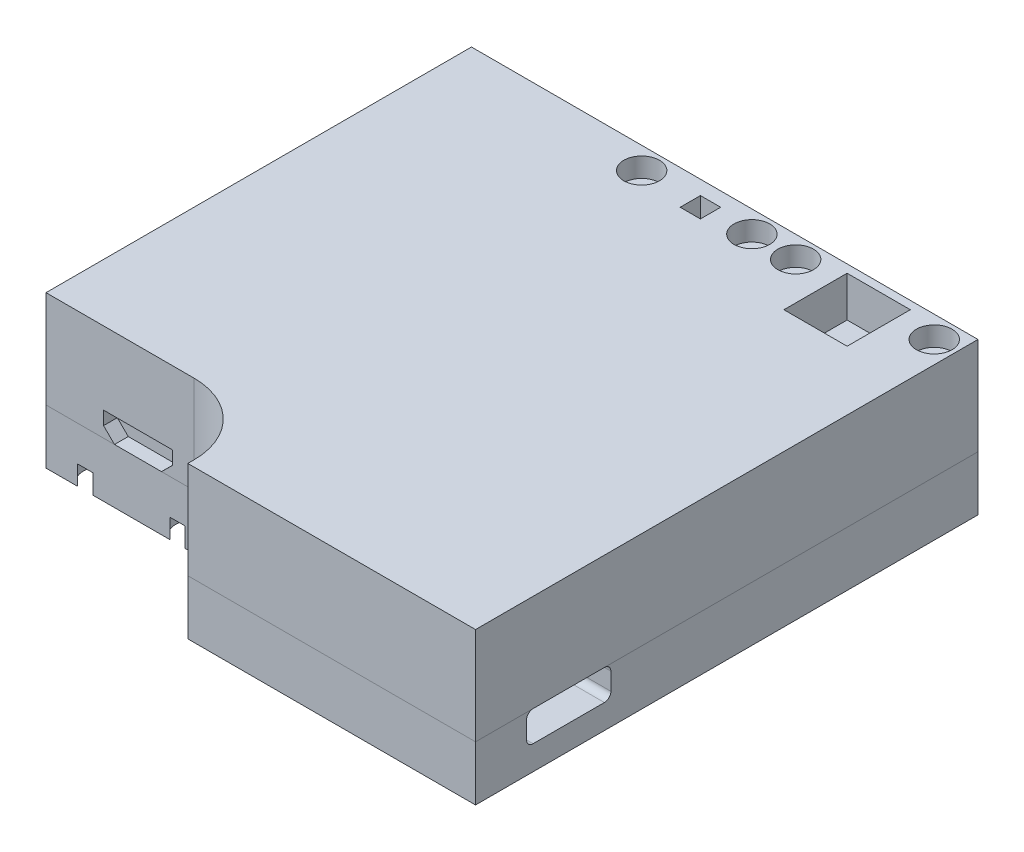
SolidWorks part; units mm, degrees
ref_plane "Front Plane" through (0, 0, 0) normal (0, 0, 1) x (1, 0, 0)
ref_plane "Top Plane" through (0, 0, 0) normal (0, 1, 0) x (1, 0, 0)
ref_plane "Right Plane" through (0, 0, 0) normal (1, 0, 0) x (0, 0, -1)
sketch "Sketch2" plane through (0, 0, 0) normal (0, 1, 0) x (1, 0, 0)
  line L0 (0, 62) -> (0, 0)
  line L1 (-62.5, 62) -> (0, 62)
  line L2 (-62.5, 62) -> (-62.5, 9.5)
  line L4 (0, 62) -> (0, 0)
  line L5 (0, 0) -> (-35.5, 0)
  line L6 (-35.5, 0) -> (-35.5, 9.5)
  line L7 (-35.5, 9.5) -> (-62.5, 9.5)
  dimension "D1" = 52.5
  dimension "D2" = 62.5
  dimension "D3" = 62
  dimension "D4" = 35.5
  dimension "D5" = 9.5
  dimension "D6" = 27
extrude "Boss-Extrude1" add sketch "Sketch2" along normal blind 12 and the other way blind 6.75 contours L7 L6 L5 L0 L1 L2
sketch "Sketch5" plane through (0, 12, 0) normal (0, 1, 0) x (1, 0, 0)
  line L0 (-57.7, 62) -> (-57.7, 60)
  line L1 (-62.5, 62) -> (0, 62) construction
  line L2 (-57.7, 60) -> (-62.5, 60)
  line L3 (-62.5, 62) -> (-62.5, 9.5) construction
  line L4 (-57.7, 60) -> (-46.3, 60)
  line L5 (-46.3, 60) -> (-46.3, 62)
  line L6 (-46.3, 60) -> (-41.5, 60)
  line L7 (-41.5, 60) -> (-41.5, 61.5)
  line L8 (-38.8, 62) -> (-38.8, 59.3)
  line L9 (-38.8, 59.3) -> (-41.5, 59.3)
  line L10 (-41.5, 59.3) -> (-41.5, 60)
  line L11 (-38.8, 59.3) -> (-25.2, 59.3)
  line L12 (-25.2, 59.3) -> (-25.2, 62)
  line L13 (-25.2, 59.3) -> (-22.5, 59.3)
  line L14 (-22.5, 59.3) -> (-22.5, 62)
  line L15 (-22.5, 59.3) -> (-19.8, 59.3)
  line L16 (-19.8, 59.3) -> (-19.8, 62)
  line L17 (-62.5, 62) -> (0, 62) construction
  line L18 (-19.8, 59.3) -> (-2.7, 59.3)
  line L19 (-2.7, 59.3) -> (-2.7, 61.5)
  line L20 (-2.7, 59.3) -> (0, 59.3)
  line L21 (0, 62) -> (0, 0) construction
  line L22 (-57.7, 60) -> (-57.7, 9.5)
  line L23 (-35.5, 9.5) -> (-62.5, 9.5) construction
  line L24 (-46.3, 60) -> (-46.3, 9.5)
  line L25 (-62.5, 11.5) -> (-57.7, 11.5)
  line L26 (-57.7, 11.5) -> (-46.3, 11.5)
  line L27 (0, 0) -> (-2.5, 0)
  line L28 (0, 0) -> (-35.5, 0) construction
  line L29 (-2.5, 0) -> (-2.5, 2.5)
  line L30 (-2.5, 2.5) -> (0, 2.5)
  line L31 (0, 62) -> (0, 0) construction
  line L32 (-2.5, 2.5) -> (-32.5, 2.5)
  line L33 (-32.5, 2.5) -> (-32.5, 0)
  line L34 (-32.5, 2.5) -> (-35, 2.5)
  line L35 (-35, 2.5) -> (-35, 0)
  line L36 (-2.5, 2.5) -> (-2.5, 20.5)
  line L37 (-2.5, 20.5) -> (0, 20.5)
  line L38 (-2.5, 20.5) -> (-2.5, 23)
  line L39 (-2.5, 23) -> (0, 23)
  line L40 (-41.5, 59.3) -> (-32, 59.3)
  line L41 (-19.8, 59.3) -> (-11.25, 59.3)
  line L42 (-19.8, 59.3) -> (-4.159, 59.3)
  line L43 (-11.25, 62) -> (-11.25, 61)
  line L44 (-22.5, 59.3) -> (-8.5, 59.3)
  line L45 (0, 59.3) -> (-14, 59.3)
  line L46 (-15.15, 53.2) -> (-15.15, 61)
  line L47 (-15.15, 53.2) -> (-7.35, 53.2)
  line L48 (-15.15, 61) -> (-7.35, 61)
  line L49 (-7.35, 53.2) -> (-7.35, 61)
  line L50 (-11.25, 61) -> (-11.25, 53.2) construction
  line L51 (-15.15, 57.1) -> (-7.35, 57.1) construction
  line L52 (-31.25, 62) -> (-31.25, 59)
  line L54 (-30, 57.75) -> (-32.5, 57.75)
  line L55 (-30, 57.75) -> (-30, 60.25)
  line L56 (-30, 60.25) -> (-32.5, 60.25)
  line L57 (-32.5, 57.75) -> (-32.5, 60.25)
  line L58 (-30, 57.75) -> (-32.5, 60.25) construction
  line L59 (-30, 60.25) -> (-32.5, 57.75) construction
  point P60 (-11.25, 57.1)
  point P68 (0, 0)
  dimension "D1" = 2
  dimension "D2" = 4.8
  dimension "D3" = 11.4
  dimension "D4" = 2
  dimension "D5" = 4.8
  dimension "D6" = 21
  dimension "D7" = 2.7
  dimension "D8" = 2.7
  dimension "D9" = 2.7
  dimension "D10" = 13.6
  dimension "D11" = 2.7
  dimension "D12" = 2.7
  dimension "D13" = 19
  dimension "D14" = 2.7
  dimension "D15" = 2.7
  dimension "D16" = 22.5
  dimension "D17" = 2
  dimension "D18" = 2.5
  dimension "D19" = 2.5
  dimension "D20" = 30
  dimension "D21" = 2.5
  dimension "D22" = 35
  dimension "D23" = 18
  dimension "D24" = 2.5
  dimension "D25" = 23
  dimension "D26" = 1
  dimension "D27" = 14
  dimension "D28" = 14
  dimension "D29" = 7.8
  dimension "D30" = 7.8
  dimension "D31" = 3
  dimension "D32" = 2.5
  dimension "D33" = 2.5
  dimension "D34" = 4.25
extrude "Cut-Extrude1" cut sketch "Sketch5" against normal mid plane 10 contours L57 L56 L55 L54 | L46 L47 L49 L48
sketch "Sketch16" plane through (0, 12, 0) normal (0, 1, 0) x (1, 0, 0)
  line L0 (0, 0) -> (0, 11.5)
  line L1 (0, 62) -> (0, 0) construction
  dimension "D1" = 11.5
sketch "Sketch17" plane through (0, 0, 0) normal (1, 0, 0) x (0, 0, -1)
  line L0 (11.5, 12) -> (11.5, -6.75)
  line L1 (0, 12) -> (11.5, 12) construction
  line L2 (62, -6.75) -> (0, -6.75) construction
  line L3 (62, 0) -> (0, 0) construction
  line L4 (6.3, -3.75) -> (16.7, -3.75)
  line L5 (6.3, -3.75) -> (6.3, 0)
  line L6 (6.3, 0) -> (16.7, 0)
  line L7 (16.7, -3.75) -> (16.7, 0)
  line L8 (6.3, 0) -> (16.7, -3.75) construction
  point P6 (11.5, 0)
  point P13 (11.5, -1.875)
  dimension "D1" = 3.75
  dimension "D2" = 10.4
  dimension "D3" = 11.5
extrude "Cut-Extrude2" cut sketch "Sketch17" against normal mid plane 10 contours L4 L7 L6 L0
fillet "Fillet6" radius 0.8 4 edges at (-2.5, -3.75, -16.7) (-2.5, -3.75, -6.3) (-2.5, 0, -16.7) (-2.5, 0, -6.3)
sketch "Sketch18" plane through (0, 12, 0) normal (0, 1, 0) x (1, 0, 0)
  line L0 (-62.5, 9.5) -> (-49, 9.5)
  line L1 (-35.5, 9.5) -> (-62.5, 9.5) construction
sketch "Sketch20" plane through (0, 0, -9.5) normal (0, 0, 1) x (1, 0, 0)
  line L0 (-62.5, 12) -> (-55.75, 12)
  line L1 (-62.5, 12) -> (-52, 12)
  line L3 (-62.5, 12) -> (-49, 12) construction
  line L4 (-52, 12) -> (-52, 8.8584)
  line L5 (-55.4, 3) -> (-52, 3)
  line L6 (-52, 3) -> (-46.9, 3)
  line L7 (-52, 3) -> (-52, 0)
  line L8 (-46.9, 3) -> (-55.4, 3)
  line L9 (-46.9, 3) -> (-46.9, 0)
  line L10 (-55.4, 3) -> (-55.4, 0)
  line L11 (-46.9, 0) -> (-55.4, 0)
  line L12 (-55.4, 3) -> (-55.4, 1.34)
  line L13 (-55.4, 1.34) -> (-54.05, 0)
  line L14 (-46.9, 3) -> (-46.9, 1.34)
  line L15 (-46.9, 1.34) -> (-48.25, 0)
  line L16 (-52, 8.8584) -> (-62.5, 8.8584)
  line L17 (-62.5, -6.75) -> (-62.5, 12) construction
  line L18 (-62.5, 8.8584) -> (-62.5, 12)
  line L20 (-62.5, 0) -> (0, 0) construction
  dimension "D1" = 8.5
  dimension "D2" = 3.4
  dimension "D3" = 3
  dimension "D4" = 5.8
  dimension "D5" = 1.66
  dimension "D6" = 1.66
  dimension "D7" = 10.5
  dimension "D8" = 3.1416
extrude "Cut-Extrude3" cut sketch "Sketch20" against normal mid plane 3.4 contours L10 L13 L11 L7 L5 | L15 L9 L6 L7 L11
fillet "Fillet4" radius 8.75 1 edges at (-35.5, 2.625, -9.5)
ref_plane "Plane7" through (0, 0, 0) normal (0, 1, 0) x (1, 0, 0)
hole_wizard "CBORE for M2 Hex Socket Head Cap Screw1" positions "3DSketch1" profile "Sketch26" counterbore size "M2" standard "DIN"
sketch3d "3DSketch1"
  point P0 (-2.7, 12, -59.3)
  point P3 (-19.8, 12, -59.3)
  point P6 (-25.2, 12, -59.3)
  point P9 (-38.8, 12, -59.3)
sketch "Sketch26" plane through (-2.7, 12, -59.3) normal (1, 0, 0) x (0, 0, 1)
  line L0 (0, 0) -> (0, 14)
  line L1 (0, 14) -> (1.2, 14)
  line L2 (1.2, 14) -> (1.2, 2.4)
  line L3 (1.2, 2.4) -> (2.2, 2.4)
  line L4 (2.2, 2.4) -> (2.2, 0)
  line L5 (2.2, 0) -> (0, 0)
  line L10 (0, 14) -> (-1.2, 14) construction
  line L11 (0, -6.35) -> (0, 107.95) construction
  dimension "Hole Dia." = 2.4
  dimension "Hole Depth" = 14
  dimension "C'Bore Dia." = 4.4
  dimension "C'Bore Depth" = 2.4
  dimension "Drill Angle" = 180
hole_wizard "CBORE for M2 Hex Socket Head Cap Screw2" positions "3DSketch2" profile "Sketch27" counterbore size "M2" standard "DIN"
sketch3d "3DSketch2"
  point P0 (-57.7436, -6.75, -60.036)
  point P2 (-46.2945, -6.75, -60.0059)
  point P4 (-46.2881, -6.75, -11.4893)
  point P6 (-57.6752, -6.75, -11.4764)
  point P8 (-32.4999, -6.75, -2.5134)
  point P10 (-2.4998, -6.75, -2.4997)
  point P12 (-2.4988, -6.75, -20.5009)
sketch "Sketch27" plane through (-57.7436, -6.75, -60.036) normal (1, 0, 0) x (0, 0, -1)
  line L0 (0, 0) -> (0, 14)
  line L1 (0, 14) -> (1.2, 14)
  line L2 (1.2, 14) -> (1.2, 2.4)
  line L3 (1.2, 2.4) -> (2.2, 2.4)
  line L4 (2.2, 2.4) -> (2.2, 0)
  line L5 (2.2, 0) -> (0, 0)
  line L10 (0, 14) -> (-1.2, 14) construction
  line L11 (0, -6.35) -> (0, 107.95) construction
  dimension "Hole Dia." = 2.4
  dimension "Hole Depth" = 14
  dimension "C'Bore Dia." = 4.4
  dimension "C'Bore Depth" = 2.4
  dimension "Drill Angle" = 180
split "Split1" trim tools "Plane7" bodies to split 112 resulting bodies 107 108
